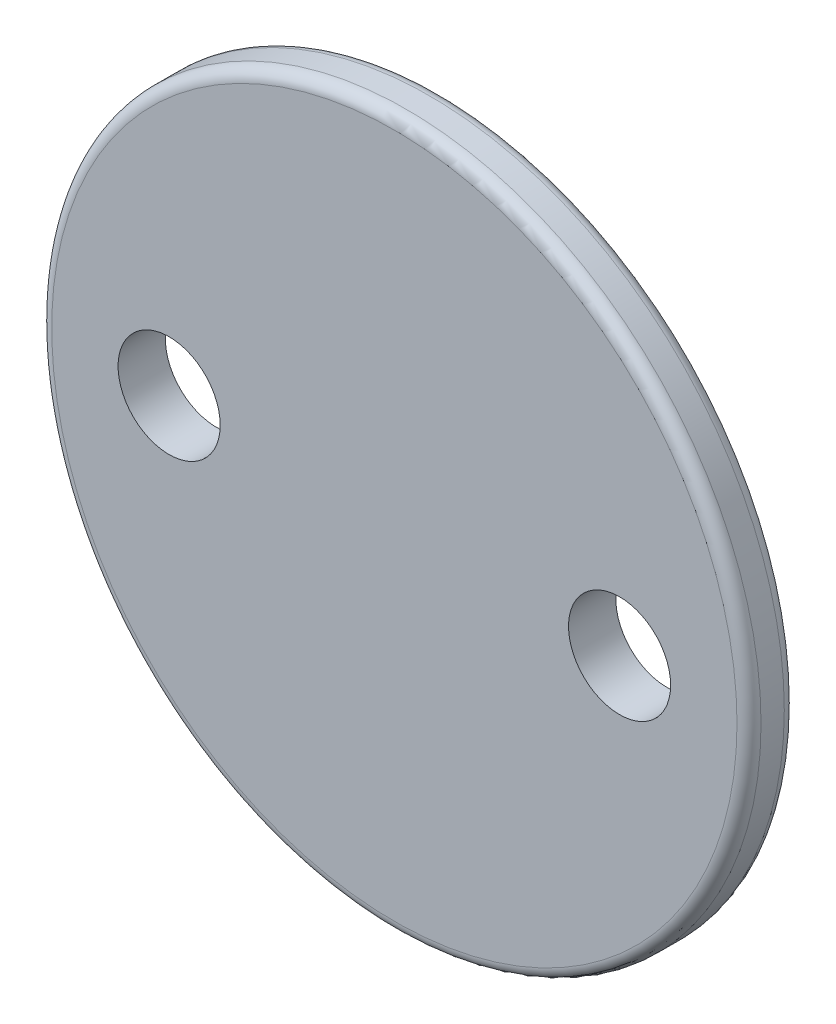
SolidWorks part; units mm, degrees
material "ABS"
ref_plane "Front Plane" through (0, 0, 0) normal (0, 0, 1) x (1, 0, 0)
ref_plane "Top Plane" through (0, 0, 0) normal (0, 1, 0) x (1, 0, 0)
ref_plane "Right Plane" through (0, 0, 0) normal (1, 0, 0) x (0, 0, -1)
sketch "Sketch1" plane through (0, 0, 0) normal (0, 0, 1) x (1, 0, 0)
  circle A0 centre (0, 0) radius 2.5
  circle A1 centre (0, 0) radius 4.5
  dimension "D2" = 5
  dimension "D1" = 2
extrude "Boss-Extrude1" add sketch "Sketch1" along normal blind 2.5
sketch "Sketch2" plane through (0, 0, 2.5) normal (0, 0, 1) x (1, 0, 0)
  circle A0 centre (0, 0) radius 15
  dimension "D1" = 30
extrude "Boss-Extrude2" add sketch "Sketch2" along normal blind 2
sketch "Sketch3" plane through (0, 0, 4.5) normal (0, 0, 1) x (1, 0, 0)
  line L0 (-9.525, 0) -> (9.525, 0) construction
  circle A0 centre (-9.525, 0) radius 2.159
  circle A1 centre (9.525, 0) radius 2.159
  point P4 (0, 0)
  dimension "D1" = 4.318
  dimension "D2" = 4.318
  dimension "D3" = 19.05
extrude "Cut-Extrude1" cut sketch "Sketch3" against normal through all both and the other way through all
fillet "Fillet2" radius 0.508 2 edges at (15, 0, 2.5) (15, 0, 4.5)
